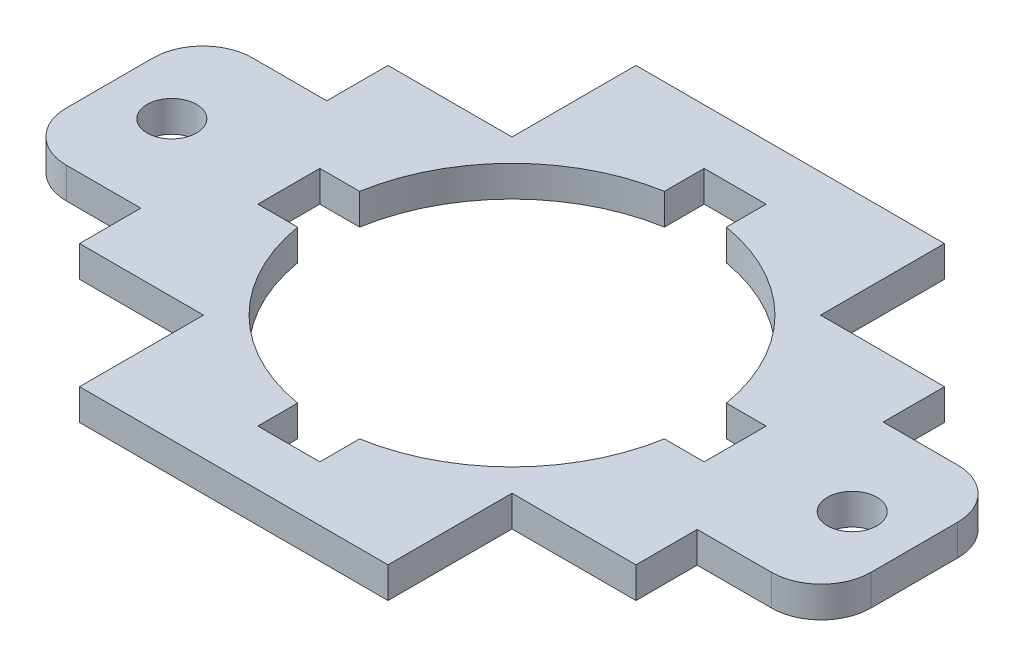
SolidWorks part; units mm, degrees
ref_plane "Front Plane" through (0, 0, 0) normal (0, 0, 1) x (1, 0, 0)
ref_plane "Top Plane" through (0, 0, 0) normal (0, 1, 0) x (1, 0, 0)
ref_plane "Right Plane" through (0, 0, 0) normal (1, 0, 0) x (0, 0, -1)
sketch "Sketch1" plane through (0, 0, 0) normal (0, 1, 0) x (1, 0, 0)
  line L5 (-15.8, 28.5) -> (-51.6907, 28.5) construction
  line L6 (15.8, -28.5) -> (-15.8, -28.5)
  line L18 (-18.7836, 3.175) -> (-22.86, 3.175)
  line L19 (22.86, -3.175) -> (18.7836, -3.175)
  line L29 (22.86, -3.175) -> (22.86, 3.175)
  line L30 (22.86, 3.175) -> (18.7836, 3.175)
  line L31 (-22.86, -3.175) -> (-22.86, 3.175)
  line L32 (28.5, -15.8) -> (28.5, -9.525)
  line L33 (22.86, -3.175) -> (-22.86, 3.175) construction
  line L34 (15.8, 28.5) -> (-15.8, 28.5)
  line L35 (-28.5, -15.8) -> (-28.5, -9.525)
  line L36 (22.86, 3.175) -> (-22.86, -3.175) construction
  line L37 (15.8, -15.8) -> (-15.8, 15.8) construction
  line L38 (3.175, -22.86) -> (-3.175, -22.86)
  line L39 (3.175, -22.86) -> (3.175, -18.7836)
  line L40 (3.175, 22.86) -> (-3.175, 22.86)
  line L41 (-3.175, -22.86) -> (-3.175, -18.7836)
  line L42 (3.175, -22.86) -> (-3.175, 22.86) construction
  line L43 (3.175, 22.86) -> (-3.175, -22.86) construction
  line L44 (-18.7836, -3.175) -> (-22.86, -3.175)
  line L45 (-3.175, 18.7836) -> (-3.175, 22.86)
  line L46 (3.175, 18.7836) -> (3.175, 22.86)
  line L47 (15.8, 15.8) -> (-15.8, -15.8) construction
  line L50 (-28.5, 15.8) -> (-15.8, 15.8)
  line L51 (-15.8, 28.5) -> (-15.8, 15.8)
  line L54 (28.5, 15.8) -> (15.8, 15.8)
  line L55 (15.8, 28.5) -> (15.8, 15.8)
  line L58 (28.5, -15.8) -> (15.8, -15.8)
  line L59 (15.8, -28.5) -> (15.8, -15.8)
  line L62 (-28.5, -15.8) -> (-15.8, -15.8)
  line L63 (-15.8, -28.5) -> (-15.8, -15.8)
  line L64 (-28.5, 9.525) -> (-36.12, 9.525)
  line L66 (-28.5, -9.525) -> (-36.12, -9.525)
  line L67 (-41.2, 4.445) -> (-41.2, -4.445)
  line L68 (-15.8, -28.5) -> (-51.6907, -28.5) construction
  line L69 (-41.2, -9.525) -> (-41.2, -28.5) construction
  line L70 (-41.2, 9.525) -> (-41.2, 28.5) construction
  line L71 (0, 22.86) -> (0, 28.5) construction
  line L72 (0, -22.86) -> (0, -28.5) construction
  line L73 (28.5, -9.525) -> (36.12, -9.525)
  line L74 (41.2, 4.445) -> (41.2, -4.445)
  line L75 (28.5, 9.525) -> (36.12, 9.525)
  line L77 (-28.5, 9.525) -> (-28.5, 15.8)
  line L78 (28.5, 9.525) -> (28.5, 15.8)
  arc A16 (-18.7836, -3.175) -> (-3.175, -18.7836) centre (0, 0) ccw
  arc A17 (-3.175, 18.7836) -> (-18.7836, 3.175) centre (0, 0) ccw
  arc A18 (18.7836, 3.175) -> (3.175, 18.7836) centre (0, 0) ccw
  arc A19 (3.175, -18.7836) -> (18.7836, -3.175) centre (0, 0) ccw
  circle A20 centre (-34.85, 0) radius 2.54
  arc A21 (-41.2, -4.445) -> (-36.12, -9.525) centre (-36.12, -4.445) ccw
  arc A22 (-36.12, 9.525) -> (-41.2, 4.445) centre (-36.12, 4.445) ccw
  circle A23 centre (34.85, 0) radius 2.54
  arc A24 (41.2, -4.445) -> (36.12, -9.525) centre (36.12, -4.445) cw
  arc A25 (36.12, 9.525) -> (41.2, 4.445) centre (36.12, 4.445) cw
  point P38 (0, 0)
  point P46 (0.0023, -3.5921)
  dimension "D5" = 6.35
  dimension "D6" = 57
  dimension "D15" = 5.08
  dimension "D18" = 5.08
  dimension "D2" = 12.7
  dimension "D3" = 12.7
  dimension "D7" = 12.7
  dimension "D9" = 19.05
  dimension "D11" = 57
  dimension "D12" = 31.6
  dimension "D10" = 6.35
  dimension "D8" = 12.7
  dimension "D14" = 5.64
  dimension "D16" = 6.35
  dimension "D17" = 9.525
extrude "Boss-Extrude1" add sketch "Sketch1" along normal blind 3.175
